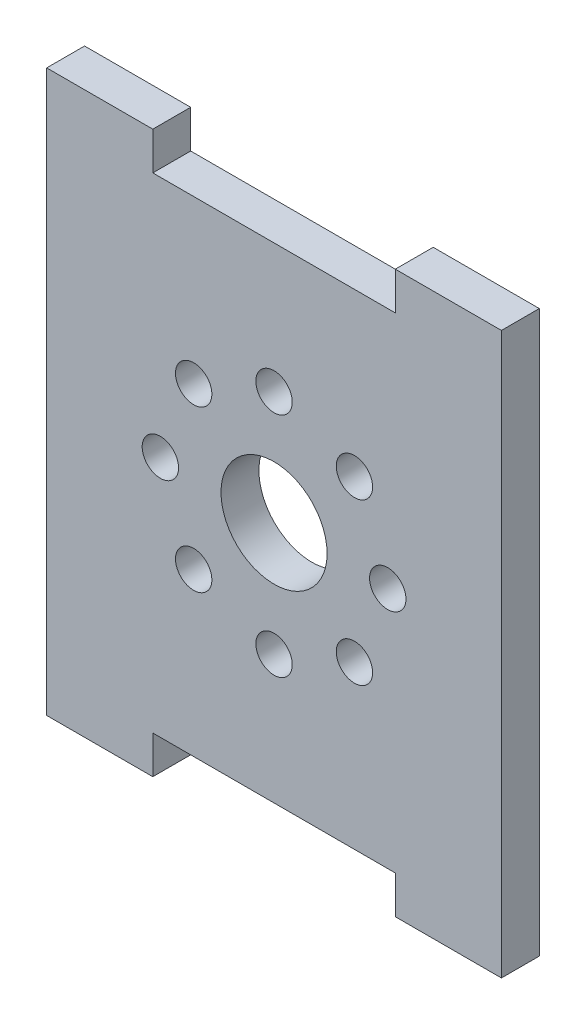
SolidWorks part; units mm, degrees
material "Acero aleado (SS)"
ref_plane "Alzado" through (0, 0, 0) normal (0, 0, 1) x (1, 0, 0)
ref_plane "Planta" through (0, 0, 0) normal (0, 1, 0) x (1, 0, 0)
ref_plane "Vista lateral" through (0, 0, 0) normal (1, 0, 0) x (0, 0, -1)
sketch "Croquis1" plane through (0, 0, 0) normal (0, 0, 1) x (1, 0, 0)
  line L0 (-15, 18.5) -> (-8, 18.5)
  line L1 (-8, 18.5) -> (-8, 16)
  line L2 (-15, -18.5) -> (-15, 18.5)
  line L3 (-8, 16) -> (8, 16)
  line L4 (15, -18.5) -> (15, 18.5)
  line L5 (-15, -18.5) -> (15, 18.5) construction
  line L6 (-15, 18.5) -> (15, -18.5) construction
  line L7 (8, 16) -> (8, 18.5)
  line L8 (8, 18.5) -> (15, 18.5)
  line L10 (-8, -18.5) -> (-8, -16)
  line L11 (8, -16) -> (8, -18.5)
  line L12 (8, -18.5) -> (15, -18.5)
  line L13 (-8, -16) -> (8, -16)
  line L14 (-15, -18.5) -> (-8, -18.5)
  circle A0 centre (0, 0) radius 3.5
  circle A1 centre (0, 7.5) radius 1.2
  circle A2 centre (5.3033, 5.3033) radius 1.2
  circle A3 centre (7.5, 0) radius 1.2
  circle A4 centre (5.3033, -5.3033) radius 1.2
  circle A5 centre (0, -7.5) radius 1.2
  circle A6 centre (-5.3033, -5.3033) radius 1.2
  circle A7 centre (-7.5, 0) radius 1.2
  circle A8 centre (-5.3033, 5.3033) radius 1.2
  point P33 (0, 0)
  dimension "D1" = 7
  dimension "D7" = 2.4
  dimension "D8" = 7.5
  dimension "D2" = 37
  dimension "D3" = 30
  dimension "D4" = 7
  dimension "D5" = 2.5
  dimension "D6" = 16
  dimension "D9" = 8
extrude "Saliente-Extruir1" add sketch "Croquis1" along normal mid plane 2.5
